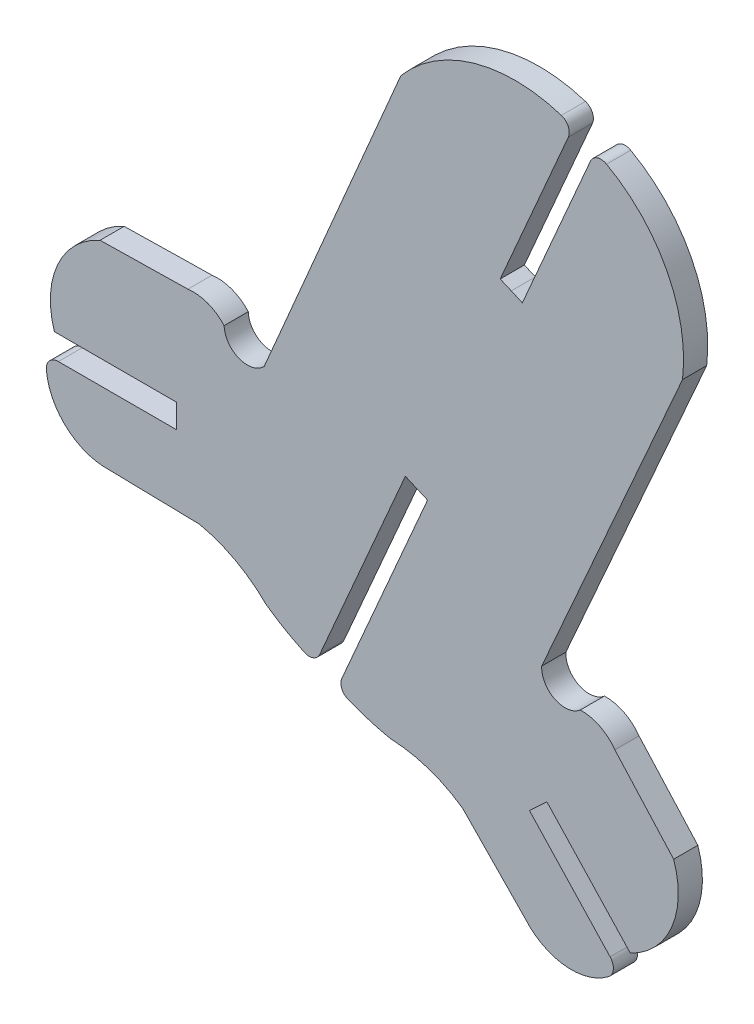
SolidWorks part; units mm, degrees
ref_plane "Front Plane" through (0, 0, 0) normal (0, 0, 1) x (1, 0, 0)
ref_plane "Top Plane" through (0, 0, 0) normal (0, 1, 0) x (1, 0, 0)
ref_plane "Right Plane" through (0, 0, 0) normal (1, 0, 0) x (0, 0, -1)
sketch "Sketch1" plane through (0, 0, 0) normal (0, 0, 1) x (1, 0, 0)
  line L0 (-11.698, 1.3011) -> (-17.242, 1.2003)
  line L1 (-16.6362, -11.0621) -> (-10.9721, -11.1826)
  line L2 (10.96, -15.3901) -> (16.2254, -21.0296)
  line L3 (-12.4086, -5.2377) -> (-12.4086, -6.742)
  line L4 (-3.3771, -14.5077) -> (2.0302, -2.0612)
  line L5 (2.0302, -2.0612) -> (2.7291, -2.365)
  line L6 (9.8605, -16.4167) -> (14.9537, -21.8718)
  line L7 (10.6353, -8.135) -> (19.5233, 11.9678)
  line L8 (9.4117, 11.1046) -> (13.7113, 21.0014)
  line L9 (8.7146, 11.4124) -> (8.0139, 11.7119)
  line L10 (8.0139, 11.7119) -> (12.3136, 21.6086)
  line L11 (8.7146, 11.4124) -> (9.4117, 11.1046)
  line L12 (-6.884, -0.5237) -> (1.7443, 19.6919)
  line L13 (-12.4086, -6.742) -> (-19.8718, -6.742)
  line L14 (-12.4086, -5.2377) -> (-19.8718, -5.2377) construction
  line L15 (2.7291, -2.365) -> (8.7146, 11.4124) construction
  line L16 (3.428, -2.6685) -> (2.7291, -2.365)
  line L17 (-1.9793, -15.115) -> (3.428, -2.6685)
  line L18 (-12.4086, -5.2377) -> (-20.1241, -5.2377)
  line L19 (10.96, -15.3901) -> (9.8605, -16.4167)
  line L20 (9.5878, -22.455) -> (5.6343, -18.3972)
  line L21 (15.2545, -10.4084) -> (18.9642, -14.5295)
  arc A0 (-9.4113, 0.4494) -> (-6.884, -0.5237) centre (-7.9408, 0.5001) ccw
  arc A1 (-9.4113, 0.4494) -> (-11.698, 1.3011) centre (-11.3563, -1.2771) ccw
  arc A2 (-20.6305, -7.5751) -> (-16.6362, -11.0621) centre (-16.7977, -7.2158) ccw
  arc A3 (-6.7541, -13.4723) -> (-10.9721, -11.1826) centre (-12.754, -19.4948) ccw
  arc A4 (-6.7541, -13.4723) -> (-4.3465, -14.8746) centre (2.2064, -0.8561) ccw
  arc A5 (14.9537, -21.8718) -> (14.8625, -22.9949) centre (14.3967, -22.3918) cw
  arc A6 (-1.586, -16.074) -> (-1.9793, -15.115) centre (-1.3161, -15.4031) cw
  arc A7 (13.7113, 21.0014) -> (14.7252, 21.3456) centre (14.3745, 20.7132) cw
  arc A8 (14.7252, 21.3456) -> (19.5233, 11.9678) centre (10.1438, 13.0852) cw
  arc A9 (18.9642, -14.5295) -> (16.2254, -21.0296) centre (13.9791, -16.256) cw
  arc A10 (1.0821, -16.8768) -> (-1.586, -16.074) centre (4.1887, -1.7173) cw
  arc A11 (1.0821, -16.8768) -> (5.6343, -18.3972) centre (0.7747, -25.3723) cw
  arc A12 (-17.242, 1.2003) -> (-20.1241, -5.2377) centre (-15.1019, -3.6219) ccw
  arc A13 (11.8732, 22.5846) -> (1.7443, 19.6919) centre (8.962, 13.5987) ccw
  arc A14 (14.8625, -22.9949) -> (9.5878, -22.455) centre (12.5094, -19.9482) cw
  arc A15 (13.0714, -9.3182) -> (15.2545, -10.4084) centre (13.1368, -11.918) cw
  arc A16 (12.3136, 21.6086) -> (11.8732, 22.5846) centre (11.6504, 21.8967) ccw
  arc A17 (-4.3465, -14.8746) -> (-3.3771, -14.5077) centre (-4.0403, -14.2196) ccw
  arc A18 (13.0714, -9.3182) -> (10.6353, -8.135) centre (12.1049, -8.2087) cw
  arc A19 (-19.8718, -6.742) -> (-20.6305, -7.5751) centre (-19.8718, -7.504) ccw
extrude "Boss-Extrude1" add sketch "Sketch1" along normal blind 1.524
